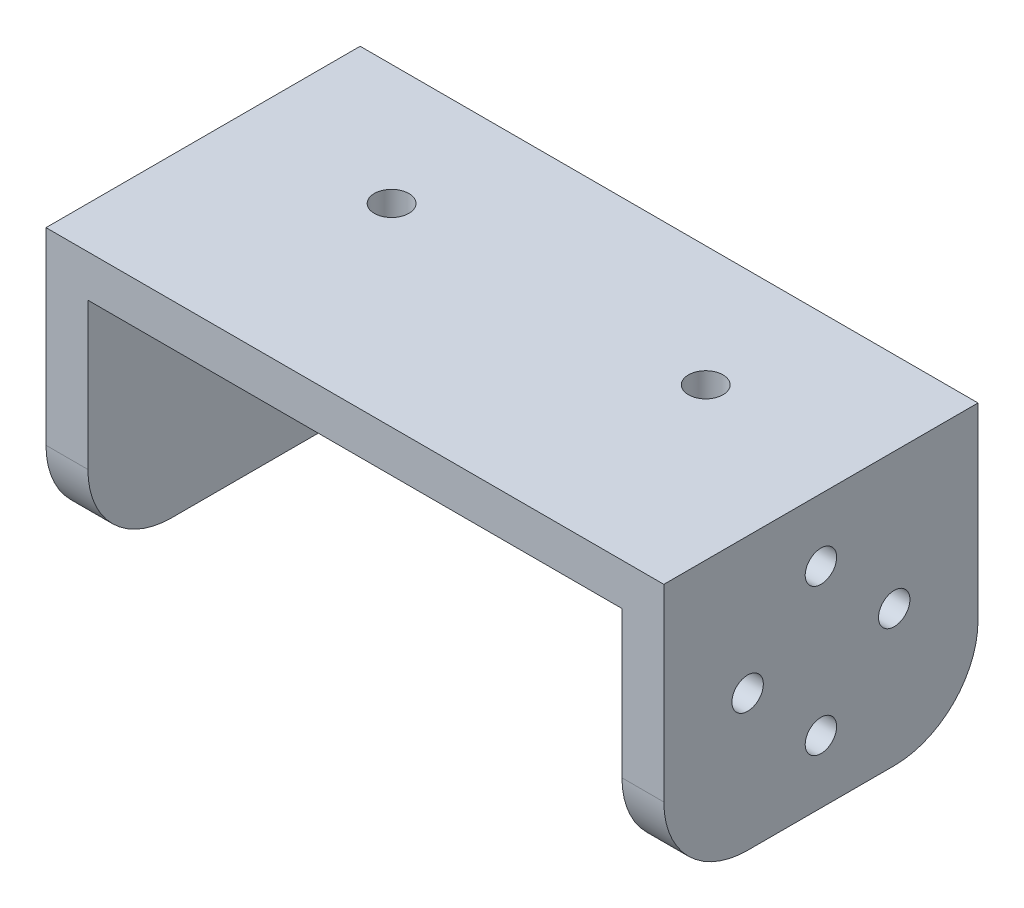
SolidWorks part; units mm, degrees
ref_plane "前视基准面" through (0, 0, 0) normal (0, 0, 1) x (1, 0, 0)
ref_plane "上视基准面" through (0, 0, 0) normal (0, 1, 0) x (1, 0, 0)
ref_plane "右视基准面" through (0, 0, 0) normal (1, 0, 0) x (0, 0, -1)
sketch "草图1" plane through (0, 0, 0) normal (0, 0, 1) x (1, 0, 0)
  line L0 (0, 0) -> (29.5, 0)
  line L1 (29.5, 0) -> (29.5, -26)
  line L2 (0, -4) -> (25.5, -4)
  line L3 (25.5, -4) -> (25.5, -26)
  line L4 (25.5, -26) -> (29.5, -26)
  line L5 (0, 0) -> (0, -6.7603) construction
  line L6 (-25.5, -26) -> (-29.5, -26)
  line L7 (-29.5, 0) -> (-29.5, -26)
  line L8 (-25.5, -4) -> (-25.5, -26)
  line L9 (0, -4) -> (-25.5, -4)
  line L10 (0, 0) -> (-29.5, 0)
  dimension "D1" = 29.5
  dimension "D3" = 26
  dimension "D2" = 4
extrude "凸台-拉伸1" add sketch "草图1" along normal blind 30
sketch "草图3" plane through (29.5, 0, 0) normal (1, 0, 0) x (0, 0, -1)
  line L3 (-30, -13) -> (-15, -13) construction
  line L5 (-30, -26) -> (-30, 0) construction
  line L6 (-15, -13) -> (0, -13) construction
  line L9 (0, -26) -> (0, 0) construction
  circle A0 centre (-15, -13) radius 10
  dimension "D1" = 20
fillet "圆角1" radius 8 4 edges at (-27.5, -26, 30) (-27.5, -26, 0) (27.5, -26, 0) (27.5, -26, 30)
sketch "草图4" plane through (0, 0, 0) normal (0, 1, 0) x (1, 0, 0)
  line L0 (0, 0) -> (0, -31.9875) construction
  line L1 (29.5, 0) -> (-29.5, 0) construction
  circle A0 centre (15, -11.5) radius 1.65
  circle A1 centre (-15, -11.5) radius 1.65
  dimension "D1" = 3.3
  dimension "D2" = 15
  dimension "D3" = 11.5
extrude "切除-拉伸1" cut sketch "草图4" against normal blind 10
sketch "草图5" plane through (-29.5, 0, 0) normal (-1, 0, 0) x (0, 0, 1)
  circle A0 centre (15, -13) radius 10 construction
  circle A1 centre (15, -13) radius 10 construction
  circle A2 centre (15, -13) radius 1.65
  dimension "D1" = 3.3
extrude "切除-拉伸2" cut sketch "草图5" against normal blind 10
sketch "草图6" plane through (29.5, 0, 0) normal (1, 0, 0) x (0, 0, -1)
  line L0 (-15, -13) -> (-15, -6) construction
  line L1 (-15, -13) -> (-15, -20) construction
  line L2 (-22, -13) -> (-8, -13) construction
  line L3 (-30, -13) -> (-15, -13) construction
  line L4 (-15, -13) -> (0, -13) construction
  circle A0 centre (-15, -13) radius 7 construction
  circle A1 centre (-15, -6) radius 1.5
  circle A2 centre (-8, -13) radius 1.5
  circle A3 centre (-15, -20) radius 1.5
  circle A4 centre (-22, -13) radius 1.5
  dimension "D1" = 14
  dimension "D2" = 3
extrude "切除-拉伸3" cut sketch "草图6" against normal blind 10
